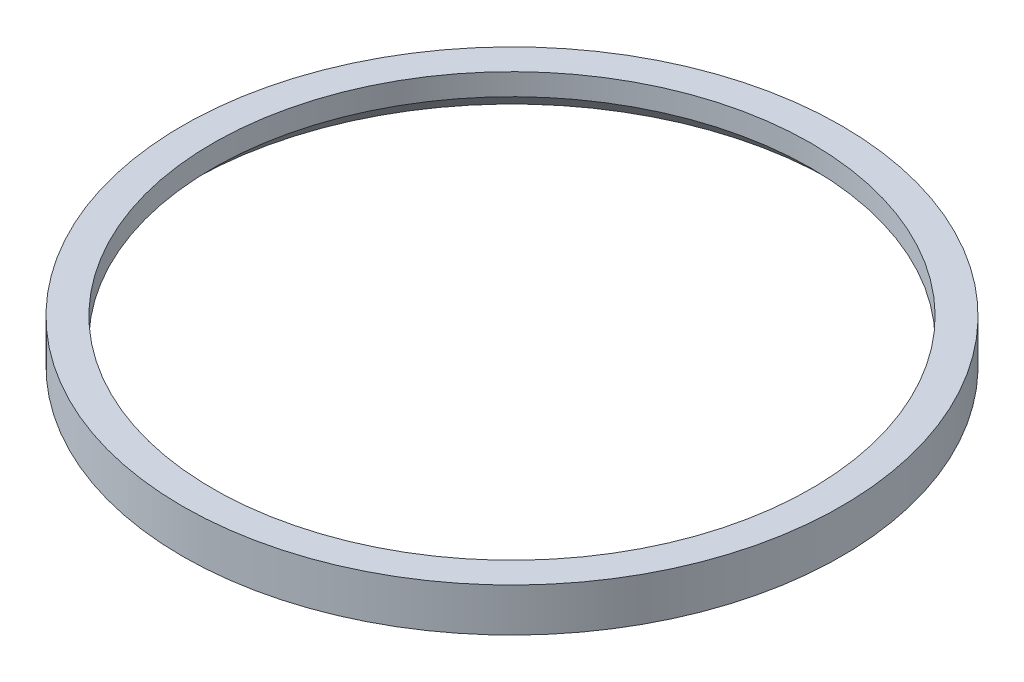
SolidWorks part; units mm, degrees
ref_plane "Front Plane" through (0, 0, 0) normal (0, 0, 1) x (1, 0, 0)
ref_plane "Top Plane" through (0, 0, 0) normal (0, 1, 0) x (1, 0, 0)
ref_plane "Right Plane" through (0, 0, 0) normal (1, 0, 0) x (0, 0, -1)
sketch "Sketch1" plane through (0, 0, 0) normal (1, 0, 0) x (0, 0, -1)
  line L0 (0, 0) -> (0, 14.4042) construction
  line L1 (18.5, 0) -> (19, 0)
  line L2 (19, 0) -> (19, 2.5)
  line L3 (19, 2.5) -> (17.25, 2.5)
  line L4 (17.25, 2.5) -> (17.25, 1.25)
  line L5 (17.25, 1.25) -> (18.5, 0)
  dimension "D1" = 19
  dimension "D2" = 2.5
  dimension "D3" = 1.75
  dimension "D4" = 1.25
  dimension "D5" = 45
revolve "Revolve1" add sketch "Sketch1" angle 360 about L0
